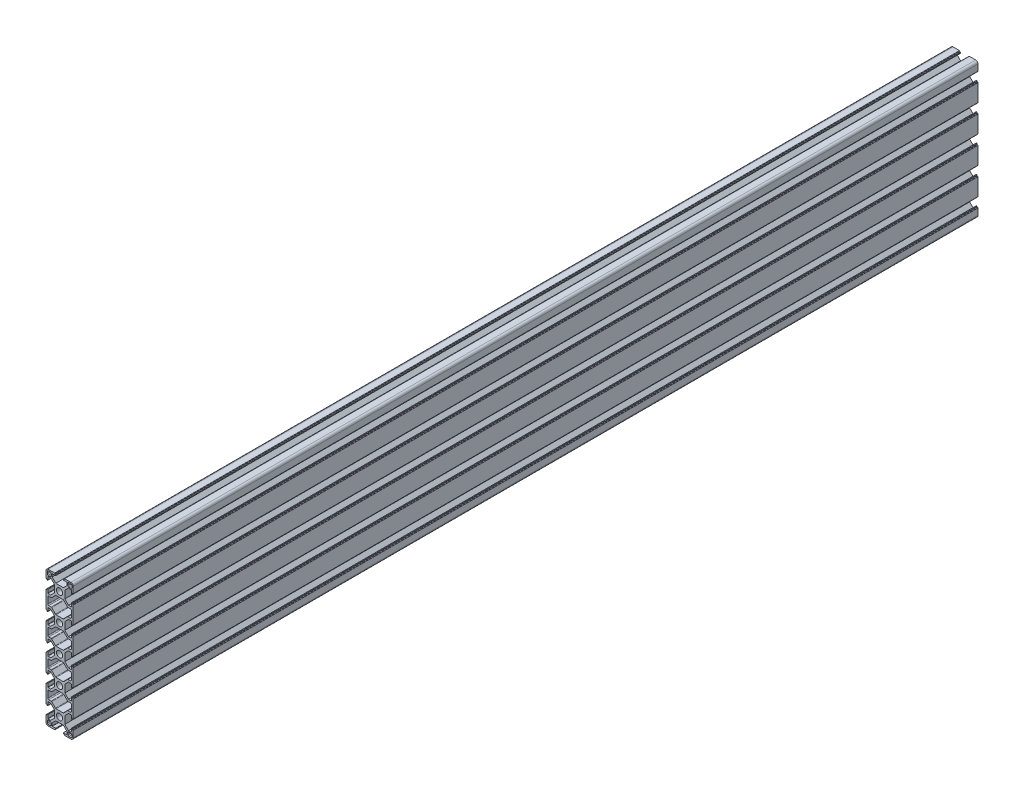
SolidWorks part; units mm, degrees
material "6063 T5"
ref_plane "Спереди" through (0, 0, 0) normal (0, 0, 1) x (1, 0, 0)
ref_plane "Сверху" through (0, 0, 0) normal (0, 1, 0) x (1, 0, 0)
ref_plane "Справа" through (0, 0, 0) normal (1, 0, 0) x (0, 0, -1)
sketch "Эскиз1" plane through (0, 0, 0) normal (0, 0, 1) x (1, 0, 0)
  line L0 (42.4804, 14.8887) -> (42.4804, -45.1113) construction
  line L1 (-15, 8.25) -> (-15, 12.5)
  line L2 (-12.5, 15) -> (-8.25, 15)
  line L3 (8.25, 15) -> (12.5, 15)
  line L4 (15, 12.5) -> (15, 8.25)
  line L5 (12.55, 9.35) -> (10.35, 9.35)
  line L6 (-12.55, 13.55) -> (-10.35, 13.55)
  line L7 (-13.55, 12.55) -> (-13.55, 10.35)
  line L8 (-12.55, 9.35) -> (-10.35, 9.35)
  line L9 (-9.35, 12.55) -> (-9.35, 10.35)
  line L10 (13.55, 12.55) -> (13.55, 10.35)
  line L11 (12.55, 13.55) -> (10.35, 13.55)
  line L12 (9.35, 12.55) -> (9.35, 10.35)
  line L13 (0, 0) -> (0, -30) construction
  line L14 (0, -15) -> (-22.4838, -15) construction
  line L23 (8.6958, -40.2071) -> (4.5816, -36.0929)
  line L24 (-3.8745, -35.8) -> (3.8745, -35.8)
  line L25 (-8.6958, -40.2071) -> (-4.5816, -36.0929)
  line L26 (-12, -40.5) -> (-9.4029, -40.5)
  line L27 (-15, -8.25) -> (-15, -21.75)
  line L28 (15, -8.25) -> (15, -21.75)
  line L29 (-13, -18.5) -> (-13, -11.5)
  line L30 (-12, -10.5) -> (-9.4029, -10.5)
  line L31 (-8.6958, -10.2071) -> (-4.5816, -6.0929)
  line L32 (-3.8745, -5.8) -> (3.8745, -5.8)
  line L33 (8.6958, -10.2071) -> (4.5816, -6.0929)
  line L34 (12, -10.5) -> (9.4029, -10.5)
  line L35 (13, -18.5) -> (13, -11.5)
  line L36 (12, -19.5) -> (9.4029, -19.5)
  line L37 (8.6958, -19.7929) -> (4.5816, -23.9071)
  line L38 (-3.8745, -24.2) -> (3.8745, -24.2)
  line L39 (-8.6958, -19.7929) -> (-4.5816, -23.9071)
  line L40 (-12, -19.5) -> (-9.4029, -19.5)
  line L41 (-13, -48.5) -> (-13, -41.5)
  line L42 (-12, -49.5) -> (-9.4029, -49.5)
  line L43 (-8.6958, -49.7929) -> (-4.5816, -53.9071)
  line L44 (-3.8745, -54.2) -> (3.8745, -54.2)
  line L45 (8.6958, -49.7929) -> (4.5816, -53.9071)
  line L46 (12, -49.5) -> (9.4029, -49.5)
  line L47 (13, -48.5) -> (13, -41.5)
  line L48 (12, -40.5) -> (9.4029, -40.5)
  line L49 (15, -38.25) -> (15, -51.75)
  line L50 (-15, -38.25) -> (-15, -51.75)
  line L51 (8.6958, -70.2071) -> (4.5816, -66.0929)
  line L52 (-3.8745, -65.8) -> (3.8745, -65.8)
  line L53 (-8.6958, -70.2071) -> (-4.5816, -66.0929)
  line L54 (-12, -70.5) -> (-9.4029, -70.5)
  line L55 (-13, -78.5) -> (-13, -71.5)
  line L56 (-12, -79.5) -> (-9.4029, -79.5)
  line L57 (-8.6958, -79.7929) -> (-4.5816, -83.9071)
  line L58 (-3.8745, -84.2) -> (3.8745, -84.2)
  line L59 (8.6958, -79.7929) -> (4.5816, -83.9071)
  line L60 (12, -79.5) -> (9.4029, -79.5)
  line L61 (13, -78.5) -> (13, -71.5)
  line L62 (12, -70.5) -> (9.4029, -70.5)
  line L63 (15, -68.25) -> (15, -81.75)
  line L64 (-15, -68.25) -> (-15, -81.75)
  line L65 (8.6958, -100.2071) -> (4.5816, -96.0929)
  line L66 (-3.8745, -95.8) -> (3.8745, -95.8)
  line L67 (-8.6958, -100.2071) -> (-4.5816, -96.0929)
  line L68 (-12, -100.5) -> (-9.4029, -100.5)
  line L69 (-13, -108.5) -> (-13, -101.5)
  line L70 (-12, -109.5) -> (-9.4029, -109.5)
  line L71 (-8.6958, -109.7929) -> (-4.5816, -113.9071)
  line L72 (-3.8745, -114.2) -> (3.8745, -114.2)
  line L73 (8.6958, -109.7929) -> (4.5816, -113.9071)
  line L74 (12, -109.5) -> (9.4029, -109.5)
  line L75 (13, -108.5) -> (13, -101.5)
  line L76 (12, -100.5) -> (9.4029, -100.5)
  line L77 (15, -98.25) -> (15, -111.75)
  line L78 (-15, -98.25) -> (-15, -111.75)
  line L79 (-15, 8.25) -> (-15, -21.75) construction
  line L80 (13.55, -132.55) -> (13.55, -130.35)
  line L81 (12.55, -129.35) -> (10.35, -129.35)
  line L82 (9.35, -132.55) -> (9.35, -130.35)
  line L83 (12.55, -133.55) -> (10.35, -133.55)
  line L84 (15, -132.5) -> (15, -128.25)
  line L85 (8.25, -135) -> (12.5, -135)
  line L86 (-12.55, -133.55) -> (-10.35, -133.55)
  line L87 (-13.55, -132.55) -> (-13.55, -130.35)
  line L88 (-12.55, -129.35) -> (-10.35, -129.35)
  line L89 (-9.35, -132.55) -> (-9.35, -130.35)
  line L90 (-12.5, -135) -> (-8.25, -135)
  line L91 (-15, -128.25) -> (-15, -132.5)
  line L92 (-27.3833, 15.012) -> (-27.149, -134.9878) construction
  arc A0 (12.5, 15) -> (15, 12.5) centre (12.5, 12.5) cw
  arc A1 (-15, 12.5) -> (-12.5, 15) centre (-12.5, 12.5) cw
  arc A2 (-13.55, 10.35) -> (-12.55, 9.35) centre (-12.55, 10.35) ccw
  arc A3 (-10.35, 9.35) -> (-9.35, 10.35) centre (-10.35, 10.35) ccw
  arc A4 (-10.35, 13.55) -> (-9.35, 12.55) centre (-10.35, 12.55) cw
  arc A5 (-12.55, 13.55) -> (-13.55, 12.55) centre (-12.55, 12.55) ccw
  arc A6 (10.35, 9.35) -> (9.35, 10.35) centre (10.35, 10.35) cw
  arc A7 (13.55, 10.35) -> (12.55, 9.35) centre (12.55, 10.35) cw
  arc A8 (12.55, 13.55) -> (13.55, 12.55) centre (12.55, 12.55) cw
  arc A9 (10.35, 13.55) -> (9.35, 12.55) centre (10.35, 12.55) ccw
  circle A10 centre (0, 0) radius 3.4
  circle A20 centre (0, -30) radius 3.4
  arc A21 (4.5816, -36.0929) -> (3.8745, -35.8) centre (3.8745, -36.8) ccw
  arc A22 (-4.5816, -6.0929) -> (-3.8745, -5.8) centre (-3.8745, -6.8) cw
  arc A23 (-9.4029, -10.5) -> (-8.6958, -10.2071) centre (-9.4029, -9.5) ccw
  arc A24 (-13, -11.5) -> (-12, -10.5) centre (-12, -11.5) cw
  arc A25 (4.5816, -6.0929) -> (3.8745, -5.8) centre (3.8745, -6.8) ccw
  arc A26 (9.4029, -10.5) -> (8.6958, -10.2071) centre (9.4029, -9.5) cw
  arc A27 (13, -11.5) -> (12, -10.5) centre (12, -11.5) ccw
  arc A28 (13, -18.5) -> (12, -19.5) centre (12, -18.5) cw
  arc A29 (9.4029, -19.5) -> (8.6958, -19.7929) centre (9.4029, -20.5) ccw
  arc A30 (4.5816, -23.9071) -> (3.8745, -24.2) centre (3.8745, -23.2) cw
  arc A31 (-4.5816, -23.9071) -> (-3.8745, -24.2) centre (-3.8745, -23.2) ccw
  arc A32 (-9.4029, -19.5) -> (-8.6958, -19.7929) centre (-9.4029, -20.5) cw
  arc A33 (-13, -18.5) -> (-12, -19.5) centre (-12, -18.5) ccw
  arc A34 (-4.5816, -36.0929) -> (-3.8745, -35.8) centre (-3.8745, -36.8) cw
  arc A35 (-9.4029, -40.5) -> (-8.6958, -40.2071) centre (-9.4029, -39.5) ccw
  arc A36 (-13, -41.5) -> (-12, -40.5) centre (-12, -41.5) cw
  arc A37 (-13, -48.5) -> (-12, -49.5) centre (-12, -48.5) ccw
  arc A38 (-9.4029, -49.5) -> (-8.6958, -49.7929) centre (-9.4029, -50.5) cw
  arc A39 (-4.5816, -53.9071) -> (-3.8745, -54.2) centre (-3.8745, -53.2) ccw
  arc A40 (4.5816, -53.9071) -> (3.8745, -54.2) centre (3.8745, -53.2) cw
  arc A41 (9.4029, -49.5) -> (8.6958, -49.7929) centre (9.4029, -50.5) ccw
  arc A42 (13, -48.5) -> (12, -49.5) centre (12, -48.5) cw
  arc A43 (13, -41.5) -> (12, -40.5) centre (12, -41.5) ccw
  arc A44 (9.4029, -40.5) -> (8.6958, -40.2071) centre (9.4029, -39.5) cw
  circle A45 centre (0, -60) radius 3.4
  arc A46 (4.5816, -66.0929) -> (3.8745, -65.8) centre (3.8745, -66.8) ccw
  arc A47 (-4.5816, -66.0929) -> (-3.8745, -65.8) centre (-3.8745, -66.8) cw
  arc A48 (-9.4029, -70.5) -> (-8.6958, -70.2071) centre (-9.4029, -69.5) ccw
  arc A49 (-13, -71.5) -> (-12, -70.5) centre (-12, -71.5) cw
  arc A50 (-13, -78.5) -> (-12, -79.5) centre (-12, -78.5) ccw
  arc A51 (-9.4029, -79.5) -> (-8.6958, -79.7929) centre (-9.4029, -80.5) cw
  arc A52 (-4.5816, -83.9071) -> (-3.8745, -84.2) centre (-3.8745, -83.2) ccw
  arc A53 (4.5816, -83.9071) -> (3.8745, -84.2) centre (3.8745, -83.2) cw
  arc A54 (9.4029, -79.5) -> (8.6958, -79.7929) centre (9.4029, -80.5) ccw
  arc A55 (13, -78.5) -> (12, -79.5) centre (12, -78.5) cw
  arc A56 (13, -71.5) -> (12, -70.5) centre (12, -71.5) ccw
  arc A57 (9.4029, -70.5) -> (8.6958, -70.2071) centre (9.4029, -69.5) cw
  circle A58 centre (0, -90) radius 3.4
  arc A59 (4.5816, -96.0929) -> (3.8745, -95.8) centre (3.8745, -96.8) ccw
  arc A60 (-4.5816, -96.0929) -> (-3.8745, -95.8) centre (-3.8745, -96.8) cw
  arc A61 (-9.4029, -100.5) -> (-8.6958, -100.2071) centre (-9.4029, -99.5) ccw
  arc A62 (-13, -101.5) -> (-12, -100.5) centre (-12, -101.5) cw
  arc A63 (-13, -108.5) -> (-12, -109.5) centre (-12, -108.5) ccw
  arc A64 (-9.4029, -109.5) -> (-8.6958, -109.7929) centre (-9.4029, -110.5) cw
  arc A65 (-4.5816, -113.9071) -> (-3.8745, -114.2) centre (-3.8745, -113.2) ccw
  arc A66 (4.5816, -113.9071) -> (3.8745, -114.2) centre (3.8745, -113.2) cw
  arc A67 (9.4029, -109.5) -> (8.6958, -109.7929) centre (9.4029, -110.5) ccw
  arc A68 (13, -108.5) -> (12, -109.5) centre (12, -108.5) cw
  arc A69 (13, -101.5) -> (12, -100.5) centre (12, -101.5) ccw
  arc A70 (9.4029, -100.5) -> (8.6958, -100.2071) centre (9.4029, -99.5) cw
  arc A71 (12.55, -133.55) -> (13.55, -132.55) centre (12.55, -132.55) ccw
  arc A72 (13.55, -130.35) -> (12.55, -129.35) centre (12.55, -130.35) ccw
  arc A73 (10.35, -129.35) -> (9.35, -130.35) centre (10.35, -130.35) ccw
  arc A74 (10.35, -133.55) -> (9.35, -132.55) centre (10.35, -132.55) cw
  arc A75 (12.5, -135) -> (15, -132.5) centre (12.5, -132.5) ccw
  circle A76 centre (0, -120) radius 3.4
  arc A77 (-10.35, -133.55) -> (-9.35, -132.55) centre (-10.35, -132.55) ccw
  arc A78 (-12.55, -133.55) -> (-13.55, -132.55) centre (-12.55, -132.55) cw
  arc A79 (-13.55, -130.35) -> (-12.55, -129.35) centre (-12.55, -130.35) cw
  arc A80 (-10.35, -129.35) -> (-9.35, -130.35) centre (-10.35, -130.35) cw
  arc A81 (-15, -132.5) -> (-12.5, -135) centre (-12.5, -132.5) ccw
  point P2 (-15, -15)
  point P4 (0, 0)
  point P24 (-9.35, 13.55)
  point P27 (-13.55, 13.55)
  point P46 (15, -15)
  point P77 (0, -30)
  point P100 (0, -5.8)
  point P110 (13, -15)
  point P127 (-13, -15)
  line B0 (-15, 8.25) -> (-15, 5.5)
  line B1 (-14.7, 5.2) -> (-14.3, 5.2)
  line B2 (-14, 4.9) -> (-14, 4.4)
  line B3 (-13.7, 4.1) -> (-13.3, 4.1)
  line B4 (-13, 4.4) -> (-13, 7.95)
  line B5 (-12.7, 8.25) -> (-9.85, 8.25)
  line B6 (-9.85, 8.25) -> (-5.8, 4.2)
  line B7 (-5.8, 0) -> (-15, 0) construction
  line B8 (-5.8, -4.2) -> (-5.8, 4.2)
  line B9 (-9.85, -8.25) -> (-5.8, -4.2)
  line B10 (-12.7, -8.25) -> (-9.85, -8.25)
  line B11 (-13, -4.4) -> (-13, -7.95)
  line B12 (-13.7, -4.1) -> (-13.3, -4.1)
  line B13 (-14, -4.9) -> (-14, -4.4)
  line B14 (-14.7, -5.2) -> (-14.3, -5.2)
  line B15 (-15, -8.25) -> (-15, -5.5)
  arc B16 (-13, 7.95) -> (-12.7, 8.25) centre (-12.7, 7.95) cw
  arc B17 (-13.3, 4.1) -> (-13, 4.4) centre (-13.3, 4.4) ccw
  arc B18 (-14, 4.4) -> (-13.7, 4.1) centre (-13.7, 4.4) ccw
  arc B19 (-14.3, 5.2) -> (-14, 4.9) centre (-14.3, 4.9) cw
  arc B20 (-15, 5.5) -> (-14.7, 5.2) centre (-14.7, 5.5) ccw
  arc B21 (-15, -5.5) -> (-14.7, -5.2) centre (-14.7, -5.5) cw
  arc B22 (-14.3, -5.2) -> (-14, -4.9) centre (-14.3, -4.9) ccw
  arc B23 (-14, -4.4) -> (-13.7, -4.1) centre (-13.7, -4.4) cw
  arc B24 (-13.3, -4.1) -> (-13, -4.4) centre (-13.3, -4.4) cw
  arc B25 (-13, -7.95) -> (-12.7, -8.25) centre (-12.7, -7.95) ccw
  line B26 (8.25, 15) -> (5.5, 15)
  line B27 (5.2, 14.7) -> (5.2, 14.3)
  line B28 (4.9, 14) -> (4.4, 14)
  line B29 (4.1, 13.7) -> (4.1, 13.3)
  line B30 (4.4, 13) -> (7.95, 13)
  line B31 (8.25, 12.7) -> (8.25, 9.85)
  line B32 (8.25, 9.85) -> (4.2, 5.8)
  line B33 (0, 5.8) -> (0, 15) construction
  line B34 (-4.2, 5.8) -> (4.2, 5.8)
  line B35 (-8.25, 9.85) -> (-4.2, 5.8)
  line B36 (-8.25, 12.7) -> (-8.25, 9.85)
  line B37 (-4.4, 13) -> (-7.95, 13)
  line B38 (-4.1, 13.7) -> (-4.1, 13.3)
  line B39 (-4.9, 14) -> (-4.4, 14)
  line B40 (-5.2, 14.7) -> (-5.2, 14.3)
  line B41 (-8.25, 15) -> (-5.5, 15)
  arc B42 (7.95, 13) -> (8.25, 12.7) centre (7.95, 12.7) cw
  arc B43 (4.1, 13.3) -> (4.4, 13) centre (4.4, 13.3) ccw
  arc B44 (4.4, 14) -> (4.1, 13.7) centre (4.4, 13.7) ccw
  arc B45 (5.2, 14.3) -> (4.9, 14) centre (4.9, 14.3) cw
  arc B46 (5.5, 15) -> (5.2, 14.7) centre (5.5, 14.7) ccw
  arc B47 (-5.5, 15) -> (-5.2, 14.7) centre (-5.5, 14.7) cw
  arc B48 (-5.2, 14.3) -> (-4.9, 14) centre (-4.9, 14.3) ccw
  arc B49 (-4.4, 14) -> (-4.1, 13.7) centre (-4.4, 13.7) cw
  arc B50 (-4.1, 13.3) -> (-4.4, 13) centre (-4.4, 13.3) cw
  arc B51 (-7.95, 13) -> (-8.25, 12.7) centre (-7.95, 12.7) ccw
  line B52 (15, -8.25) -> (15, -5.5)
  line B53 (14.7, -5.2) -> (14.3, -5.2)
  line B54 (14, -4.9) -> (14, -4.4)
  line B55 (13.7, -4.1) -> (13.3, -4.1)
  line B56 (13, -4.4) -> (13, -7.95)
  line B57 (12.7, -8.25) -> (9.85, -8.25)
  line B58 (9.85, -8.25) -> (5.8, -4.2)
  line B59 (5.8, 0) -> (15, 0) construction
  line B60 (5.8, 4.2) -> (5.8, -4.2)
  line B61 (9.85, 8.25) -> (5.8, 4.2)
  line B62 (12.7, 8.25) -> (9.85, 8.25)
  line B63 (13, 4.4) -> (13, 7.95)
  line B64 (13.7, 4.1) -> (13.3, 4.1)
  line B65 (14, 4.9) -> (14, 4.4)
  line B66 (14.7, 5.2) -> (14.3, 5.2)
  line B67 (15, 8.25) -> (15, 5.5)
  arc B68 (13, -7.95) -> (12.7, -8.25) centre (12.7, -7.95) cw
  arc B69 (13.3, -4.1) -> (13, -4.4) centre (13.3, -4.4) ccw
  arc B70 (14, -4.4) -> (13.7, -4.1) centre (13.7, -4.4) ccw
  arc B71 (14.3, -5.2) -> (14, -4.9) centre (14.3, -4.9) cw
  arc B72 (15, -5.5) -> (14.7, -5.2) centre (14.7, -5.5) ccw
  arc B73 (15, 5.5) -> (14.7, 5.2) centre (14.7, 5.5) cw
  arc B74 (14.3, 5.2) -> (14, 4.9) centre (14.3, 4.9) ccw
  arc B75 (14, 4.4) -> (13.7, 4.1) centre (13.7, 4.4) cw
  arc B76 (13.3, 4.1) -> (13, 4.4) centre (13.3, 4.4) cw
  arc B77 (13, 7.95) -> (12.7, 8.25) centre (12.7, 7.95) ccw
  line B78 (-15, -21.75) -> (-15, -24.5)
  line B79 (-14.7, -24.8) -> (-14.3, -24.8)
  line B80 (-14, -25.1) -> (-14, -25.6)
  line B81 (-13.7, -25.9) -> (-13.3, -25.9)
  line B82 (-13, -25.6) -> (-13, -22.05)
  line B83 (-12.7, -21.75) -> (-9.85, -21.75)
  line B84 (-9.85, -21.75) -> (-5.8, -25.8)
  line B85 (-5.8, -30) -> (-15, -30) construction
  line B86 (-5.8, -34.2) -> (-5.8, -25.8)
  line B87 (-9.85, -38.25) -> (-5.8, -34.2)
  line B88 (-12.7, -38.25) -> (-9.85, -38.25)
  line B89 (-13, -34.4) -> (-13, -37.95)
  line B90 (-13.7, -34.1) -> (-13.3, -34.1)
  line B91 (-14, -34.9) -> (-14, -34.4)
  line B92 (-14.7, -35.2) -> (-14.3, -35.2)
  line B93 (-15, -38.25) -> (-15, -35.5)
  arc B94 (-13, -22.05) -> (-12.7, -21.75) centre (-12.7, -22.05) cw
  arc B95 (-13.3, -25.9) -> (-13, -25.6) centre (-13.3, -25.6) ccw
  arc B96 (-14, -25.6) -> (-13.7, -25.9) centre (-13.7, -25.6) ccw
  arc B97 (-14.3, -24.8) -> (-14, -25.1) centre (-14.3, -25.1) cw
  arc B98 (-15, -24.5) -> (-14.7, -24.8) centre (-14.7, -24.5) ccw
  arc B99 (-15, -35.5) -> (-14.7, -35.2) centre (-14.7, -35.5) cw
  arc B100 (-14.3, -35.2) -> (-14, -34.9) centre (-14.3, -34.9) ccw
  arc B101 (-14, -34.4) -> (-13.7, -34.1) centre (-13.7, -34.4) cw
  arc B102 (-13.3, -34.1) -> (-13, -34.4) centre (-13.3, -34.4) cw
  arc B103 (-13, -37.95) -> (-12.7, -38.25) centre (-12.7, -37.95) ccw
  line B104 (15, -38.25) -> (15, -35.5)
  line B105 (14.7, -35.2) -> (14.3, -35.2)
  line B106 (14, -34.9) -> (14, -34.4)
  line B107 (13.7, -34.1) -> (13.3, -34.1)
  line B108 (13, -34.4) -> (13, -37.95)
  line B109 (12.7, -38.25) -> (9.85, -38.25)
  line B110 (9.85, -38.25) -> (5.8, -34.2)
  line B111 (5.8, -30) -> (15, -30) construction
  line B112 (5.8, -25.8) -> (5.8, -34.2)
  line B113 (9.85, -21.75) -> (5.8, -25.8)
  line B114 (12.7, -21.75) -> (9.85, -21.75)
  line B115 (13, -25.6) -> (13, -22.05)
  line B116 (13.7, -25.9) -> (13.3, -25.9)
  line B117 (14, -25.1) -> (14, -25.6)
  line B118 (14.7, -24.8) -> (14.3, -24.8)
  line B119 (15, -21.75) -> (15, -24.5)
  arc B120 (13, -37.95) -> (12.7, -38.25) centre (12.7, -37.95) cw
  arc B121 (13.3, -34.1) -> (13, -34.4) centre (13.3, -34.4) ccw
  arc B122 (14, -34.4) -> (13.7, -34.1) centre (13.7, -34.4) ccw
  arc B123 (14.3, -35.2) -> (14, -34.9) centre (14.3, -34.9) cw
  arc B124 (15, -35.5) -> (14.7, -35.2) centre (14.7, -35.5) ccw
  arc B125 (15, -24.5) -> (14.7, -24.8) centre (14.7, -24.5) cw
  arc B126 (14.3, -24.8) -> (14, -25.1) centre (14.3, -25.1) ccw
  arc B127 (14, -25.6) -> (13.7, -25.9) centre (13.7, -25.6) cw
  arc B128 (13.3, -25.9) -> (13, -25.6) centre (13.3, -25.6) cw
  arc B129 (13, -22.05) -> (12.7, -21.75) centre (12.7, -22.05) ccw
  line B130 (-15, -51.75) -> (-15, -54.5)
  line B131 (-14.7, -54.8) -> (-14.3, -54.8)
  line B132 (-14, -55.1) -> (-14, -55.6)
  line B133 (-13.7, -55.9) -> (-13.3, -55.9)
  line B134 (-13, -55.6) -> (-13, -52.05)
  line B135 (-12.7, -51.75) -> (-9.85, -51.75)
  line B136 (-9.85, -51.75) -> (-5.8, -55.8)
  line B137 (-5.8, -60) -> (-15, -60) construction
  line B138 (-5.8, -64.2) -> (-5.8, -55.8)
  line B139 (-9.85, -68.25) -> (-5.8, -64.2)
  line B140 (-12.7, -68.25) -> (-9.85, -68.25)
  line B141 (-13, -64.4) -> (-13, -67.95)
  line B142 (-13.7, -64.1) -> (-13.3, -64.1)
  line B143 (-14, -64.9) -> (-14, -64.4)
  line B144 (-14.7, -65.2) -> (-14.3, -65.2)
  line B145 (-15, -68.25) -> (-15, -65.5)
  arc B146 (-13, -52.05) -> (-12.7, -51.75) centre (-12.7, -52.05) cw
  arc B147 (-13.3, -55.9) -> (-13, -55.6) centre (-13.3, -55.6) ccw
  arc B148 (-14, -55.6) -> (-13.7, -55.9) centre (-13.7, -55.6) ccw
  arc B149 (-14.3, -54.8) -> (-14, -55.1) centre (-14.3, -55.1) cw
  arc B150 (-15, -54.5) -> (-14.7, -54.8) centre (-14.7, -54.5) ccw
  arc B151 (-15, -65.5) -> (-14.7, -65.2) centre (-14.7, -65.5) cw
  arc B152 (-14.3, -65.2) -> (-14, -64.9) centre (-14.3, -64.9) ccw
  arc B153 (-14, -64.4) -> (-13.7, -64.1) centre (-13.7, -64.4) cw
  arc B154 (-13.3, -64.1) -> (-13, -64.4) centre (-13.3, -64.4) cw
  arc B155 (-13, -67.95) -> (-12.7, -68.25) centre (-12.7, -67.95) ccw
  line B156 (15, -68.25) -> (15, -65.5)
  line B157 (14.7, -65.2) -> (14.3, -65.2)
  line B158 (14, -64.9) -> (14, -64.4)
  line B159 (13.7, -64.1) -> (13.3, -64.1)
  line B160 (13, -64.4) -> (13, -67.95)
  line B161 (12.7, -68.25) -> (9.85, -68.25)
  line B162 (9.85, -68.25) -> (5.8, -64.2)
  line B163 (5.8, -60) -> (15, -60) construction
  line B164 (5.8, -55.8) -> (5.8, -64.2)
  line B165 (9.85, -51.75) -> (5.8, -55.8)
  line B166 (12.7, -51.75) -> (9.85, -51.75)
  line B167 (13, -55.6) -> (13, -52.05)
  line B168 (13.7, -55.9) -> (13.3, -55.9)
  line B169 (14, -55.1) -> (14, -55.6)
  line B170 (14.7, -54.8) -> (14.3, -54.8)
  line B171 (15, -51.75) -> (15, -54.5)
  arc B172 (13, -67.95) -> (12.7, -68.25) centre (12.7, -67.95) cw
  arc B173 (13.3, -64.1) -> (13, -64.4) centre (13.3, -64.4) ccw
  arc B174 (14, -64.4) -> (13.7, -64.1) centre (13.7, -64.4) ccw
  arc B175 (14.3, -65.2) -> (14, -64.9) centre (14.3, -64.9) cw
  arc B176 (15, -65.5) -> (14.7, -65.2) centre (14.7, -65.5) ccw
  arc B177 (15, -54.5) -> (14.7, -54.8) centre (14.7, -54.5) cw
  arc B178 (14.3, -54.8) -> (14, -55.1) centre (14.3, -55.1) ccw
  arc B179 (14, -55.6) -> (13.7, -55.9) centre (13.7, -55.6) cw
  arc B180 (13.3, -55.9) -> (13, -55.6) centre (13.3, -55.6) cw
  arc B181 (13, -52.05) -> (12.7, -51.75) centre (12.7, -52.05) ccw
  line B182 (-15, -81.75) -> (-15, -84.5)
  line B183 (-14.7, -84.8) -> (-14.3, -84.8)
  line B184 (-14, -85.1) -> (-14, -85.6)
  line B185 (-13.7, -85.9) -> (-13.3, -85.9)
  line B186 (-13, -85.6) -> (-13, -82.05)
  line B187 (-12.7, -81.75) -> (-9.85, -81.75)
  line B188 (-9.85, -81.75) -> (-5.8, -85.8)
  line B189 (-5.8, -90) -> (-15, -90) construction
  line B190 (-5.8, -94.2) -> (-5.8, -85.8)
  line B191 (-9.85, -98.25) -> (-5.8, -94.2)
  line B192 (-12.7, -98.25) -> (-9.85, -98.25)
  line B193 (-13, -94.4) -> (-13, -97.95)
  line B194 (-13.7, -94.1) -> (-13.3, -94.1)
  line B195 (-14, -94.9) -> (-14, -94.4)
  line B196 (-14.7, -95.2) -> (-14.3, -95.2)
  line B197 (-15, -98.25) -> (-15, -95.5)
  arc B198 (-13, -82.05) -> (-12.7, -81.75) centre (-12.7, -82.05) cw
  arc B199 (-13.3, -85.9) -> (-13, -85.6) centre (-13.3, -85.6) ccw
  arc B200 (-14, -85.6) -> (-13.7, -85.9) centre (-13.7, -85.6) ccw
  arc B201 (-14.3, -84.8) -> (-14, -85.1) centre (-14.3, -85.1) cw
  arc B202 (-15, -84.5) -> (-14.7, -84.8) centre (-14.7, -84.5) ccw
  arc B203 (-15, -95.5) -> (-14.7, -95.2) centre (-14.7, -95.5) cw
  arc B204 (-14.3, -95.2) -> (-14, -94.9) centre (-14.3, -94.9) ccw
  arc B205 (-14, -94.4) -> (-13.7, -94.1) centre (-13.7, -94.4) cw
  arc B206 (-13.3, -94.1) -> (-13, -94.4) centre (-13.3, -94.4) cw
  arc B207 (-13, -97.95) -> (-12.7, -98.25) centre (-12.7, -97.95) ccw
  line B208 (15, -98.25) -> (15, -95.5)
  line B209 (14.7, -95.2) -> (14.3, -95.2)
  line B210 (14, -94.9) -> (14, -94.4)
  line B211 (13.7, -94.1) -> (13.3, -94.1)
  line B212 (13, -94.4) -> (13, -97.95)
  line B213 (12.7, -98.25) -> (9.85, -98.25)
  line B214 (9.85, -98.25) -> (5.8, -94.2)
  line B215 (5.8, -90) -> (15, -90) construction
  line B216 (5.8, -85.8) -> (5.8, -94.2)
  line B217 (9.85, -81.75) -> (5.8, -85.8)
  line B218 (12.7, -81.75) -> (9.85, -81.75)
  line B219 (13, -85.6) -> (13, -82.05)
  line B220 (13.7, -85.9) -> (13.3, -85.9)
  line B221 (14, -85.1) -> (14, -85.6)
  line B222 (14.7, -84.8) -> (14.3, -84.8)
  line B223 (15, -81.75) -> (15, -84.5)
  arc B224 (13, -97.95) -> (12.7, -98.25) centre (12.7, -97.95) cw
  arc B225 (13.3, -94.1) -> (13, -94.4) centre (13.3, -94.4) ccw
  arc B226 (14, -94.4) -> (13.7, -94.1) centre (13.7, -94.4) ccw
  arc B227 (14.3, -95.2) -> (14, -94.9) centre (14.3, -94.9) cw
  arc B228 (15, -95.5) -> (14.7, -95.2) centre (14.7, -95.5) ccw
  arc B229 (15, -84.5) -> (14.7, -84.8) centre (14.7, -84.5) cw
  arc B230 (14.3, -84.8) -> (14, -85.1) centre (14.3, -85.1) ccw
  arc B231 (14, -85.6) -> (13.7, -85.9) centre (13.7, -85.6) cw
  arc B232 (13.3, -85.9) -> (13, -85.6) centre (13.3, -85.6) cw
  arc B233 (13, -82.05) -> (12.7, -81.75) centre (12.7, -82.05) ccw
  line B234 (15, -111.75) -> (15, -114.5)
  line B235 (14.7, -114.8) -> (14.3, -114.8)
  line B236 (14, -115.1) -> (14, -115.6)
  line B237 (13.7, -115.9) -> (13.3, -115.9)
  line B238 (13, -115.6) -> (13, -112.05)
  line B239 (12.7, -111.75) -> (9.85, -111.75)
  line B240 (9.85, -111.75) -> (5.8, -115.8)
  line B241 (5.8, -120) -> (15, -120) construction
  line B242 (5.8, -124.2) -> (5.8, -115.8)
  line B243 (9.85, -128.25) -> (5.8, -124.2)
  line B244 (12.7, -128.25) -> (9.85, -128.25)
  line B245 (13, -124.4) -> (13, -127.95)
  line B246 (13.7, -124.1) -> (13.3, -124.1)
  line B247 (14, -124.9) -> (14, -124.4)
  line B248 (14.7, -125.2) -> (14.3, -125.2)
  line B249 (15, -128.25) -> (15, -125.5)
  arc B250 (13, -112.05) -> (12.7, -111.75) centre (12.7, -112.05) ccw
  arc B251 (13.3, -115.9) -> (13, -115.6) centre (13.3, -115.6) cw
  arc B252 (14, -115.6) -> (13.7, -115.9) centre (13.7, -115.6) cw
  arc B253 (14.3, -114.8) -> (14, -115.1) centre (14.3, -115.1) ccw
  arc B254 (15, -114.5) -> (14.7, -114.8) centre (14.7, -114.5) cw
  arc B255 (15, -125.5) -> (14.7, -125.2) centre (14.7, -125.5) ccw
  arc B256 (14.3, -125.2) -> (14, -124.9) centre (14.3, -124.9) cw
  arc B257 (14, -124.4) -> (13.7, -124.1) centre (13.7, -124.4) ccw
  arc B258 (13.3, -124.1) -> (13, -124.4) centre (13.3, -124.4) ccw
  arc B259 (13, -127.95) -> (12.7, -128.25) centre (12.7, -127.95) cw
  line B260 (-15, -128.25) -> (-15, -125.5)
  line B261 (-14.7, -125.2) -> (-14.3, -125.2)
  line B262 (-14, -124.9) -> (-14, -124.4)
  line B263 (-13.7, -124.1) -> (-13.3, -124.1)
  line B264 (-13, -124.4) -> (-13, -127.95)
  line B265 (-12.7, -128.25) -> (-9.85, -128.25)
  line B266 (-9.85, -128.25) -> (-5.8, -124.2)
  line B267 (-5.8, -120) -> (-15, -120) construction
  line B268 (-5.8, -115.8) -> (-5.8, -124.2)
  line B269 (-9.85, -111.75) -> (-5.8, -115.8)
  line B270 (-12.7, -111.75) -> (-9.85, -111.75)
  line B271 (-13, -115.6) -> (-13, -112.05)
  line B272 (-13.7, -115.9) -> (-13.3, -115.9)
  line B273 (-14, -115.1) -> (-14, -115.6)
  line B274 (-14.7, -114.8) -> (-14.3, -114.8)
  line B275 (-15, -111.75) -> (-15, -114.5)
  arc B276 (-13, -127.95) -> (-12.7, -128.25) centre (-12.7, -127.95) ccw
  arc B277 (-13.3, -124.1) -> (-13, -124.4) centre (-13.3, -124.4) cw
  arc B278 (-14, -124.4) -> (-13.7, -124.1) centre (-13.7, -124.4) cw
  arc B279 (-14.3, -125.2) -> (-14, -124.9) centre (-14.3, -124.9) ccw
  arc B280 (-15, -125.5) -> (-14.7, -125.2) centre (-14.7, -125.5) cw
  arc B281 (-15, -114.5) -> (-14.7, -114.8) centre (-14.7, -114.5) ccw
  arc B282 (-14.3, -114.8) -> (-14, -115.1) centre (-14.3, -115.1) cw
  arc B283 (-14, -115.6) -> (-13.7, -115.9) centre (-13.7, -115.6) ccw
  arc B284 (-13.3, -115.9) -> (-13, -115.6) centre (-13.3, -115.6) ccw
  arc B285 (-13, -112.05) -> (-12.7, -111.75) centre (-12.7, -112.05) cw
  line B286 (8.25, -135) -> (5.5, -135)
  line B287 (5.2, -134.7) -> (5.2, -134.3)
  line B288 (4.9, -134) -> (4.4, -134)
  line B289 (4.1, -133.7) -> (4.1, -133.3)
  line B290 (4.4, -133) -> (7.95, -133)
  line B291 (8.25, -132.7) -> (8.25, -129.85)
  line B292 (8.25, -129.85) -> (4.2, -125.8)
  line B293 (0, -125.8) -> (0, -135) construction
  line B294 (-4.2, -125.8) -> (4.2, -125.8)
  line B295 (-8.25, -129.85) -> (-4.2, -125.8)
  line B296 (-8.25, -132.7) -> (-8.25, -129.85)
  line B297 (-4.4, -133) -> (-7.95, -133)
  line B298 (-4.1, -133.7) -> (-4.1, -133.3)
  line B299 (-4.9, -134) -> (-4.4, -134)
  line B300 (-5.2, -134.7) -> (-5.2, -134.3)
  line B301 (-8.25, -135) -> (-5.5, -135)
  arc B302 (7.95, -133) -> (8.25, -132.7) centre (7.95, -132.7) ccw
  arc B303 (4.1, -133.3) -> (4.4, -133) centre (4.4, -133.3) cw
  arc B304 (4.4, -134) -> (4.1, -133.7) centre (4.4, -133.7) cw
  arc B305 (5.2, -134.3) -> (4.9, -134) centre (4.9, -134.3) ccw
  arc B306 (5.5, -135) -> (5.2, -134.7) centre (5.5, -134.7) cw
  arc B307 (-5.5, -135) -> (-5.2, -134.7) centre (-5.5, -134.7) ccw
  arc B308 (-5.2, -134.3) -> (-4.9, -134) centre (-4.9, -134.3) cw
  arc B309 (-4.4, -134) -> (-4.1, -133.7) centre (-4.4, -133.7) ccw
  arc B310 (-4.1, -133.3) -> (-4.4, -133) centre (-4.4, -133.3) ccw
  arc B311 (-7.95, -133) -> (-8.25, -132.7) centre (-7.95, -132.7) cw
  dimension "D8" = 6.8
  dimension "D3" = 2.5
  dimension "D7" = 1
  dimension "D14" = 1
  dimension "D1" = 15
  dimension "D2" = 60
  dimension "D4" = 1.1
  dimension "D5" = 1.1
  dimension "D6" = 4.2
  dimension "D9" = 30
  dimension "D10" = 9
  dimension "D11" = 26
  dimension "D12" = 18.4
  dimension "D13" = 2.2
  dimension "D15" = 4
  dimension "D16" = 30
  dimension "D17" = 150
sketch_block_instance "Блок1-1"
sketch_block "Блок1" parameters "D6"=0.3, "D1"=16.5, "D2"=8.4, "D3"=9.2, "D4"=45, "D5"=10.4, "D7"=2, "D8"=1, "D9"=8.2
sketch_block_instance "Блок1-2"
sketch_block_instance "Блок1-3"
sketch_block_instance "Блок1-7"
sketch_block_instance "Блок1-8"
sketch_block_instance "Блок1-9"
sketch_block_instance "Блок1-10"
sketch_block_instance "Блок1-11"
sketch_block_instance "Блок1-12"
sketch_block_instance "Блок1-13"
sketch_block_instance "Блок1-14"
sketch_block_instance "Блок1-15"
extrude "Бобышка-Вытянуть1" add sketch "Эскиз1" along normal blind 1000
